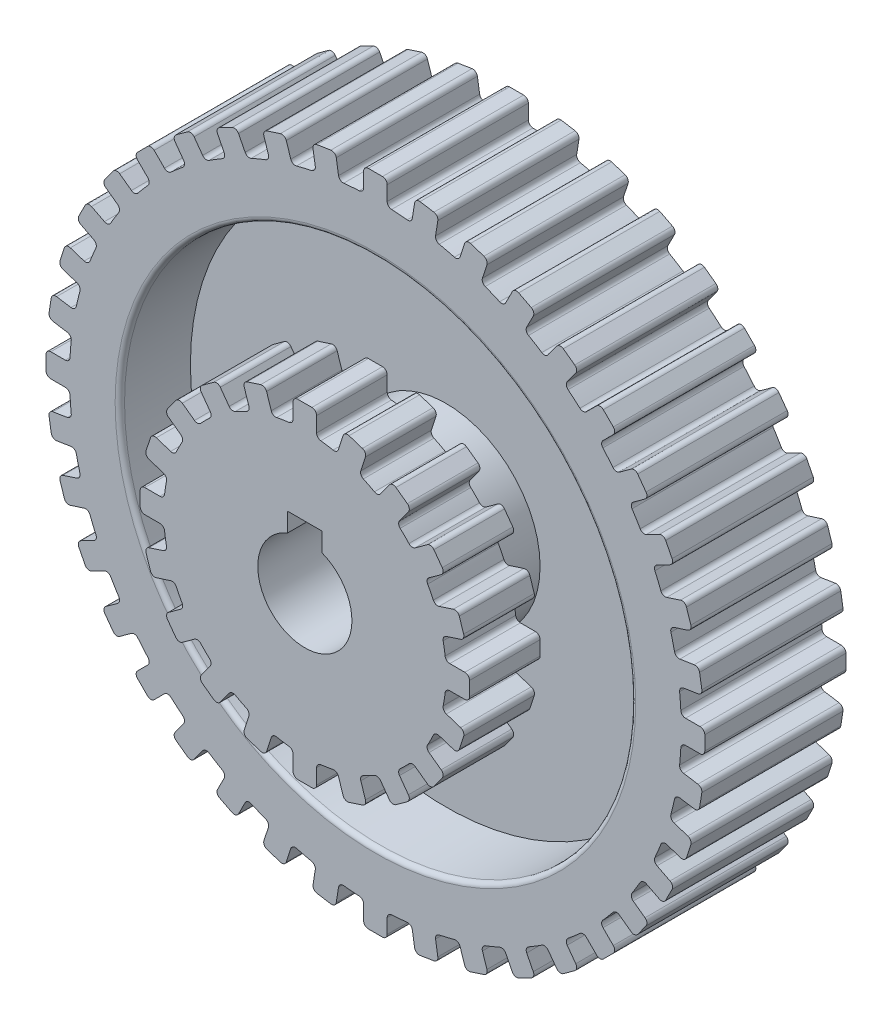
SolidWorks part; units mm, degrees
ref_plane "Front Plane" through (0, 0, 0) normal (0, 0, 1) x (1, 0, 0)
ref_plane "Top Plane" through (0, 0, 0) normal (0, 1, 0) x (1, 0, 0)
ref_plane "Right Plane" through (0, 0, 0) normal (1, 0, 0) x (0, 0, -1)
sketch "Sketch1" plane through (0, 0, 0) normal (0, 0, 1) x (1, 0, 0)
  line L0 (8.3248, 68.5416) -> (7.8409, 65.4868)
  line L1 (-1.5, 70) -> (1.5, 70)
  line L2 (2.5, 69) -> (2.5, 65.9071)
  line L3 (-2.5, 69) -> (-2.5, 65.9071)
  line L4 (9.4689, 69.3728) -> (12.4319, 68.9035)
  line L5 (13.2632, 67.7594) -> (12.7794, 64.7046)
  line L6 (18.9445, 66.3954) -> (17.9888, 63.4539)
  line L7 (20.2046, 67.0375) -> (23.0578, 66.1104)
  line L8 (23.6998, 64.8504) -> (22.7441, 61.9089)
  line L9 (29.0978, 62.6144) -> (27.6937, 59.8587)
  line L10 (30.4428, 63.0514) -> (33.1158, 61.6895)
  line L11 (33.5529, 60.3445) -> (32.1487, 57.5887)
  line L12 (38.5346, 57.2916) -> (36.7167, 54.7895)
  line L13 (39.9314, 57.5129) -> (42.3585, 55.7495)
  line L14 (42.5797, 54.3527) -> (40.7618, 51.8505)
  line L15 (47.0226, 50.5581) -> (44.8356, 48.3711)
  line L16 (48.4368, 50.5581) -> (50.5581, 48.4368)
  line L17 (50.5581, 47.0226) -> (48.3711, 44.8356)
  line L18 (54.3527, 42.5797) -> (51.8505, 40.7618)
  line L19 (55.7495, 42.3585) -> (57.5129, 39.9314)
  line L20 (57.2916, 38.5346) -> (54.7895, 36.7167)
  line L21 (60.3445, 33.5529) -> (57.5887, 32.1487)
  line L22 (61.6895, 33.1158) -> (63.0514, 30.4428)
  line L23 (62.6144, 29.0978) -> (59.8587, 27.6937)
  line L24 (64.8504, 23.6998) -> (61.9089, 22.7441)
  line L25 (66.1104, 23.0578) -> (67.0375, 20.2046)
  line L26 (66.3954, 18.9445) -> (63.4539, 17.9888)
  line L27 (67.7594, 13.2632) -> (64.7046, 12.7794)
  line L28 (68.9035, 12.4319) -> (69.3728, 9.4689)
  line L29 (68.5416, 8.3248) -> (65.4868, 7.8409)
  line L30 (69, 2.5) -> (65.9071, 2.5)
  line L31 (70, 1.5) -> (70, -1.5)
  line L32 (69, -2.5) -> (65.9071, -2.5)
  line L33 (68.5416, -8.3248) -> (65.4868, -7.8409)
  line L34 (69.3728, -9.4689) -> (68.9035, -12.4319)
  line L35 (67.7594, -13.2632) -> (64.7046, -12.7794)
  line L36 (66.3954, -18.9445) -> (63.4539, -17.9888)
  line L37 (67.0375, -20.2046) -> (66.1104, -23.0578)
  line L38 (64.8504, -23.6998) -> (61.9089, -22.7441)
  line L39 (62.6144, -29.0978) -> (59.8587, -27.6937)
  line L40 (63.0514, -30.4428) -> (61.6895, -33.1158)
  line L41 (60.3445, -33.5529) -> (57.5887, -32.1487)
  line L42 (57.2916, -38.5346) -> (54.7895, -36.7167)
  line L43 (57.5129, -39.9314) -> (55.7495, -42.3585)
  line L44 (54.3527, -42.5797) -> (51.8505, -40.7618)
  line L45 (50.5581, -47.0226) -> (48.3711, -44.8356)
  line L46 (50.5581, -48.4368) -> (48.4368, -50.5581)
  line L47 (47.0226, -50.5581) -> (44.8356, -48.3711)
  line L48 (42.5797, -54.3527) -> (40.7618, -51.8505)
  line L49 (42.3585, -55.7495) -> (39.9314, -57.5129)
  line L50 (38.5346, -57.2916) -> (36.7167, -54.7895)
  line L51 (33.5529, -60.3445) -> (32.1487, -57.5887)
  line L52 (33.1158, -61.6895) -> (30.4428, -63.0514)
  line L53 (29.0978, -62.6144) -> (27.6937, -59.8587)
  line L54 (23.6998, -64.8504) -> (22.7441, -61.9089)
  line L55 (23.0578, -66.1104) -> (20.2046, -67.0375)
  line L56 (18.9445, -66.3954) -> (17.9888, -63.4539)
  line L57 (13.2632, -67.7594) -> (12.7794, -64.7046)
  line L58 (12.4319, -68.9035) -> (9.4689, -69.3728)
  line L59 (8.3248, -68.5416) -> (7.8409, -65.4868)
  line L60 (2.5, -69) -> (2.5, -65.9071)
  line L61 (1.5, -70) -> (-1.5, -70)
  line L62 (-2.5, -69) -> (-2.5, -65.9071)
  line L63 (-8.3248, -68.5416) -> (-7.8409, -65.4868)
  line L64 (-9.4689, -69.3728) -> (-12.4319, -68.9035)
  line L65 (-13.2632, -67.7594) -> (-12.7794, -64.7046)
  line L66 (-18.9445, -66.3954) -> (-17.9888, -63.4539)
  line L67 (-20.2046, -67.0375) -> (-23.0578, -66.1104)
  line L68 (-23.6998, -64.8504) -> (-22.7441, -61.9089)
  line L69 (-29.0978, -62.6144) -> (-27.6937, -59.8587)
  line L70 (-30.4428, -63.0514) -> (-33.1158, -61.6895)
  line L71 (-33.5529, -60.3445) -> (-32.1487, -57.5887)
  line L72 (-38.5346, -57.2916) -> (-36.7167, -54.7895)
  line L73 (-39.9314, -57.5129) -> (-42.3585, -55.7495)
  line L74 (-42.5797, -54.3527) -> (-40.7618, -51.8505)
  line L75 (-47.0226, -50.5581) -> (-44.8356, -48.3711)
  line L76 (-48.4368, -50.5581) -> (-50.5581, -48.4368)
  line L77 (-50.5581, -47.0226) -> (-48.3711, -44.8356)
  line L78 (-54.3527, -42.5797) -> (-51.8505, -40.7618)
  line L79 (-55.7495, -42.3585) -> (-57.5129, -39.9314)
  line L80 (-57.2916, -38.5346) -> (-54.7895, -36.7167)
  line L81 (-60.3445, -33.5529) -> (-57.5887, -32.1487)
  line L82 (-61.6895, -33.1158) -> (-63.0514, -30.4428)
  line L83 (-62.6144, -29.0978) -> (-59.8587, -27.6937)
  line L84 (-64.8504, -23.6998) -> (-61.9089, -22.7441)
  line L85 (-66.1104, -23.0578) -> (-67.0375, -20.2046)
  line L86 (-66.3954, -18.9445) -> (-63.4539, -17.9888)
  line L87 (-67.7594, -13.2632) -> (-64.7046, -12.7794)
  line L88 (-68.9035, -12.4319) -> (-69.3728, -9.4689)
  line L89 (-68.5416, -8.3248) -> (-65.4868, -7.8409)
  line L90 (-69, -2.5) -> (-65.9071, -2.5)
  line L91 (-70, -1.5) -> (-70, 1.5)
  line L92 (-69, 2.5) -> (-65.9071, 2.5)
  line L93 (-68.5416, 8.3248) -> (-65.4868, 7.8409)
  line L94 (-69.3728, 9.4689) -> (-68.9035, 12.4319)
  line L95 (-67.7594, 13.2632) -> (-64.7046, 12.7794)
  line L96 (-66.3954, 18.9445) -> (-63.4539, 17.9888)
  line L97 (-67.0375, 20.2046) -> (-66.1104, 23.0578)
  line L98 (-64.8504, 23.6998) -> (-61.9089, 22.7441)
  line L99 (-62.6144, 29.0978) -> (-59.8587, 27.6937)
  line L100 (-63.0514, 30.4428) -> (-61.6895, 33.1158)
  line L101 (-60.3445, 33.5529) -> (-57.5887, 32.1487)
  line L102 (-57.2916, 38.5346) -> (-54.7895, 36.7167)
  line L103 (-57.5129, 39.9314) -> (-55.7495, 42.3585)
  line L104 (-54.3527, 42.5797) -> (-51.8505, 40.7618)
  line L105 (-50.5581, 47.0226) -> (-48.3711, 44.8356)
  line L106 (-50.5581, 48.4368) -> (-48.4368, 50.5581)
  line L107 (-47.0226, 50.5581) -> (-44.8356, 48.3711)
  line L108 (-42.5797, 54.3527) -> (-40.7618, 51.8505)
  line L109 (-42.3585, 55.7495) -> (-39.9314, 57.5129)
  line L110 (-38.5346, 57.2916) -> (-36.7167, 54.7895)
  line L111 (-33.5529, 60.3445) -> (-32.1487, 57.5887)
  line L112 (-33.1158, 61.6895) -> (-30.4428, 63.0514)
  line L113 (-29.0978, 62.6144) -> (-27.6937, 59.8587)
  line L114 (-23.6998, 64.8504) -> (-22.7441, 61.9089)
  line L115 (-23.0578, 66.1104) -> (-20.2046, 67.0375)
  line L116 (-18.9445, 66.3954) -> (-17.9888, 63.4539)
  line L117 (-13.2632, 67.7594) -> (-12.7794, 64.7046)
  line L118 (-12.4319, 68.9035) -> (-9.4689, 69.3728)
  line L119 (-8.3248, 68.5416) -> (-7.8409, 65.4868)
  arc A0 (-3.447, 64.9085) -> (-6.7494, 64.6486) centre (0, 0) ccw
  arc A2 (-2.5, 65.9071) -> (-3.447, 64.9085) centre (-3.5, 65.9071) cw
  arc A3 (3.447, 64.9085) -> (2.5, 65.9071) centre (3.5, 65.9071) cw
  arc A4 (1.5, 70) -> (2.5, 69) centre (1.5, 69) cw
  arc A5 (-1.5, 70) -> (-2.5, 69) centre (-1.5, 69) ccw
  arc A6 (7.8409, 65.4868) -> (6.7494, 64.6486) centre (6.8532, 65.6432) cw
  arc A7 (9.4689, 69.3728) -> (8.3248, 68.5416) centre (9.3124, 68.3851) ccw
  arc A8 (12.4319, 68.9035) -> (13.2632, 67.7594) centre (12.2755, 67.9158) cw
  arc A9 (13.5585, 63.5702) -> (12.7794, 64.7046) centre (13.7671, 64.5482) cw
  arc A10 (17.9888, 63.4539) -> (16.7796, 62.7969) centre (17.0377, 63.763) cw
  arc A11 (20.2046, 67.0375) -> (18.9445, 66.3954) centre (19.8956, 66.0864) ccw
  arc A12 (23.0578, 66.1104) -> (23.6998, 64.8504) centre (22.7488, 65.1594) cw
  arc A13 (23.3361, 60.6665) -> (22.7441, 61.9089) centre (23.6951, 61.5998) cw
  arc A14 (27.6937, 59.8587) -> (26.3966, 59.3988) centre (26.8027, 60.3127) cw
  arc A15 (30.4428, 63.0514) -> (29.0978, 62.6144) centre (29.9888, 62.1604) ccw
  arc A16 (33.1158, 61.6895) -> (33.5529, 60.3445) centre (32.6619, 60.7985) cw
  arc A17 (32.5391, 56.269) -> (32.1487, 57.5887) centre (33.0397, 57.1347) cw
  arc A18 (36.7167, 54.7895) -> (35.3636, 54.5382) centre (35.9077, 55.3772) cw
  arc A19 (39.9314, 57.5129) -> (38.5346, 57.2916) centre (39.3437, 56.7039) ccw
  arc A20 (42.3585, 55.7495) -> (42.5797, 54.3527) centre (41.7707, 54.9405) cw
  arc A21 (40.9409, 50.486) -> (40.7618, 51.8505) centre (41.5708, 51.2627) cw
  arc A22 (44.8356, 48.3711) -> (43.4599, 48.3346) centre (44.1285, 49.0783) cw
  arc A23 (48.4368, 50.5581) -> (47.0226, 50.5581) centre (47.7297, 49.851) ccw
  arc A24 (50.5581, 48.4368) -> (50.5581, 47.0226) centre (49.851, 47.7297) cw
  arc A25 (48.3346, 43.4599) -> (48.3711, 44.8356) centre (49.0783, 44.1285) cw
  arc A26 (51.8505, 40.7618) -> (50.486, 40.9409) centre (51.2627, 41.5708) cw
  arc A27 (55.7495, 42.3585) -> (54.3527, 42.5797) centre (54.9405, 41.7707) ccw
  arc A28 (57.5129, 39.9314) -> (57.2916, 38.5346) centre (56.7039, 39.3437) cw
  arc A29 (54.5382, 35.3636) -> (54.7895, 36.7167) centre (55.3772, 35.9077) cw
  arc A30 (57.5887, 32.1487) -> (56.269, 32.5391) centre (57.1347, 33.0397) cw
  arc A31 (61.6895, 33.1158) -> (60.3445, 33.5529) centre (60.7985, 32.6619) ccw
  arc A32 (63.0514, 30.4428) -> (62.6144, 29.0978) centre (62.1604, 29.9888) cw
  arc A33 (59.3988, 26.3966) -> (59.8587, 27.6937) centre (60.3127, 26.8027) cw
  arc A34 (61.9089, 22.7441) -> (60.6665, 23.3361) centre (61.5998, 23.6951) cw
  arc A35 (66.1104, 23.0578) -> (64.8504, 23.6998) centre (65.1594, 22.7488) ccw
  arc A36 (67.0375, 20.2046) -> (66.3954, 18.9445) centre (66.0864, 19.8956) cw
  arc A37 (62.7969, 16.7796) -> (63.4539, 17.9888) centre (63.763, 17.0377) cw
  arc A38 (64.7046, 12.7794) -> (63.5702, 13.5585) centre (64.5482, 13.7671) cw
  arc A39 (68.9035, 12.4319) -> (67.7594, 13.2632) centre (67.9158, 12.2755) ccw
  arc A40 (69.3728, 9.4689) -> (68.5416, 8.3248) centre (68.3851, 9.3124) cw
  arc A41 (64.6486, 6.7494) -> (65.4868, 7.8409) centre (65.6432, 6.8532) cw
  arc A42 (65.9071, 2.5) -> (64.9085, 3.447) centre (65.9071, 3.5) cw
  arc A43 (70, 1.5) -> (69, 2.5) centre (69, 1.5) ccw
  arc A44 (70, -1.5) -> (69, -2.5) centre (69, -1.5) cw
  arc A45 (64.9085, -3.447) -> (65.9071, -2.5) centre (65.9071, -3.5) cw
  arc A46 (65.4868, -7.8409) -> (64.6486, -6.7494) centre (65.6432, -6.8532) cw
  arc A47 (69.3728, -9.4689) -> (68.5416, -8.3248) centre (68.3851, -9.3124) ccw
  arc A48 (68.9035, -12.4319) -> (67.7594, -13.2632) centre (67.9158, -12.2755) cw
  arc A49 (63.5702, -13.5585) -> (64.7046, -12.7794) centre (64.5482, -13.7671) cw
  arc A50 (63.4539, -17.9888) -> (62.7969, -16.7796) centre (63.763, -17.0377) cw
  arc A51 (67.0375, -20.2046) -> (66.3954, -18.9445) centre (66.0864, -19.8956) ccw
  arc A52 (66.1104, -23.0578) -> (64.8504, -23.6998) centre (65.1594, -22.7488) cw
  arc A53 (60.6665, -23.3361) -> (61.9089, -22.7441) centre (61.5998, -23.6951) cw
  arc A54 (59.8587, -27.6937) -> (59.3988, -26.3966) centre (60.3127, -26.8027) cw
  arc A55 (63.0514, -30.4428) -> (62.6144, -29.0978) centre (62.1604, -29.9888) ccw
  arc A56 (61.6895, -33.1158) -> (60.3445, -33.5529) centre (60.7985, -32.6619) cw
  arc A57 (56.269, -32.5391) -> (57.5887, -32.1487) centre (57.1347, -33.0397) cw
  arc A58 (54.7895, -36.7167) -> (54.5382, -35.3636) centre (55.3772, -35.9077) cw
  arc A59 (57.5129, -39.9314) -> (57.2916, -38.5346) centre (56.7039, -39.3437) ccw
  arc A60 (55.7495, -42.3585) -> (54.3527, -42.5797) centre (54.9405, -41.7707) cw
  arc A61 (50.486, -40.9409) -> (51.8505, -40.7618) centre (51.2627, -41.5708) cw
  arc A62 (48.3711, -44.8356) -> (48.3346, -43.4599) centre (49.0783, -44.1285) cw
  arc A63 (50.5581, -48.4368) -> (50.5581, -47.0226) centre (49.851, -47.7297) ccw
  arc A64 (48.4368, -50.5581) -> (47.0226, -50.5581) centre (47.7297, -49.851) cw
  arc A65 (43.4599, -48.3346) -> (44.8356, -48.3711) centre (44.1285, -49.0783) cw
  arc A66 (40.7618, -51.8505) -> (40.9409, -50.486) centre (41.5708, -51.2627) cw
  arc A67 (42.3585, -55.7495) -> (42.5797, -54.3527) centre (41.7707, -54.9405) ccw
  arc A68 (39.9314, -57.5129) -> (38.5346, -57.2916) centre (39.3437, -56.7039) cw
  arc A69 (35.3636, -54.5382) -> (36.7167, -54.7895) centre (35.9077, -55.3772) cw
  arc A70 (32.1487, -57.5887) -> (32.5391, -56.269) centre (33.0397, -57.1347) cw
  arc A71 (33.1158, -61.6895) -> (33.5529, -60.3445) centre (32.6619, -60.7985) ccw
  arc A72 (30.4428, -63.0514) -> (29.0978, -62.6144) centre (29.9888, -62.1604) cw
  arc A73 (26.3966, -59.3988) -> (27.6937, -59.8587) centre (26.8027, -60.3127) cw
  arc A74 (22.7441, -61.9089) -> (23.3361, -60.6665) centre (23.6951, -61.5998) cw
  arc A75 (23.0578, -66.1104) -> (23.6998, -64.8504) centre (22.7488, -65.1594) ccw
  arc A76 (20.2046, -67.0375) -> (18.9445, -66.3954) centre (19.8956, -66.0864) cw
  arc A77 (16.7796, -62.7969) -> (17.9888, -63.4539) centre (17.0377, -63.763) cw
  arc A78 (12.7794, -64.7046) -> (13.5585, -63.5702) centre (13.7671, -64.5482) cw
  arc A79 (12.4319, -68.9035) -> (13.2632, -67.7594) centre (12.2755, -67.9158) ccw
  arc A80 (9.4689, -69.3728) -> (8.3248, -68.5416) centre (9.3124, -68.3851) cw
  arc A81 (6.7494, -64.6486) -> (7.8409, -65.4868) centre (6.8532, -65.6432) cw
  arc A82 (2.5, -65.9071) -> (3.447, -64.9085) centre (3.5, -65.9071) cw
  arc A83 (1.5, -70) -> (2.5, -69) centre (1.5, -69) ccw
  arc A84 (-1.5, -70) -> (-2.5, -69) centre (-1.5, -69) cw
  arc A85 (-3.447, -64.9085) -> (-2.5, -65.9071) centre (-3.5, -65.9071) cw
  arc A86 (-7.8409, -65.4868) -> (-6.7494, -64.6486) centre (-6.8532, -65.6432) cw
  arc A87 (-9.4689, -69.3728) -> (-8.3248, -68.5416) centre (-9.3124, -68.3851) ccw
  arc A88 (-12.4319, -68.9035) -> (-13.2632, -67.7594) centre (-12.2755, -67.9158) cw
  arc A89 (-13.5585, -63.5702) -> (-12.7794, -64.7046) centre (-13.7671, -64.5482) cw
  arc A90 (-17.9888, -63.4539) -> (-16.7796, -62.7969) centre (-17.0377, -63.763) cw
  arc A91 (-20.2046, -67.0375) -> (-18.9445, -66.3954) centre (-19.8956, -66.0864) ccw
  arc A92 (-23.0578, -66.1104) -> (-23.6998, -64.8504) centre (-22.7488, -65.1594) cw
  arc A93 (-23.3361, -60.6665) -> (-22.7441, -61.9089) centre (-23.6951, -61.5998) cw
  arc A94 (-27.6937, -59.8587) -> (-26.3966, -59.3988) centre (-26.8027, -60.3127) cw
  arc A95 (-30.4428, -63.0514) -> (-29.0978, -62.6144) centre (-29.9888, -62.1604) ccw
  arc A96 (-33.1158, -61.6895) -> (-33.5529, -60.3445) centre (-32.6619, -60.7985) cw
  arc A97 (-32.5391, -56.269) -> (-32.1487, -57.5887) centre (-33.0397, -57.1347) cw
  arc A98 (-36.7167, -54.7895) -> (-35.3636, -54.5382) centre (-35.9077, -55.3772) cw
  arc A99 (-39.9314, -57.5129) -> (-38.5346, -57.2916) centre (-39.3437, -56.7039) ccw
  arc A100 (-42.3585, -55.7495) -> (-42.5797, -54.3527) centre (-41.7707, -54.9405) cw
  arc A101 (-40.9409, -50.486) -> (-40.7618, -51.8505) centre (-41.5708, -51.2627) cw
  arc A102 (-44.8356, -48.3711) -> (-43.4599, -48.3346) centre (-44.1285, -49.0783) cw
  arc A103 (-48.4368, -50.5581) -> (-47.0226, -50.5581) centre (-47.7297, -49.851) ccw
  arc A104 (-50.5581, -48.4368) -> (-50.5581, -47.0226) centre (-49.851, -47.7297) cw
  arc A105 (-48.3346, -43.4599) -> (-48.3711, -44.8356) centre (-49.0783, -44.1285) cw
  arc A106 (-51.8505, -40.7618) -> (-50.486, -40.9409) centre (-51.2627, -41.5708) cw
  arc A107 (-55.7495, -42.3585) -> (-54.3527, -42.5797) centre (-54.9405, -41.7707) ccw
  arc A108 (-57.5129, -39.9314) -> (-57.2916, -38.5346) centre (-56.7039, -39.3437) cw
  arc A109 (-54.5382, -35.3636) -> (-54.7895, -36.7167) centre (-55.3772, -35.9077) cw
  arc A110 (-57.5887, -32.1487) -> (-56.269, -32.5391) centre (-57.1347, -33.0397) cw
  arc A111 (-61.6895, -33.1158) -> (-60.3445, -33.5529) centre (-60.7985, -32.6619) ccw
  arc A112 (-63.0514, -30.4428) -> (-62.6144, -29.0978) centre (-62.1604, -29.9888) cw
  arc A113 (-59.3988, -26.3966) -> (-59.8587, -27.6937) centre (-60.3127, -26.8027) cw
  arc A114 (-61.9089, -22.7441) -> (-60.6665, -23.3361) centre (-61.5998, -23.6951) cw
  arc A115 (-66.1104, -23.0578) -> (-64.8504, -23.6998) centre (-65.1594, -22.7488) ccw
  arc A116 (-67.0375, -20.2046) -> (-66.3954, -18.9445) centre (-66.0864, -19.8956) cw
  arc A117 (-62.7969, -16.7796) -> (-63.4539, -17.9888) centre (-63.763, -17.0377) cw
  arc A118 (-64.7046, -12.7794) -> (-63.5702, -13.5585) centre (-64.5482, -13.7671) cw
  arc A119 (-68.9035, -12.4319) -> (-67.7594, -13.2632) centre (-67.9158, -12.2755) ccw
  arc A120 (-69.3728, -9.4689) -> (-68.5416, -8.3248) centre (-68.3851, -9.3124) cw
  arc A121 (-64.6486, -6.7494) -> (-65.4868, -7.8409) centre (-65.6432, -6.8532) cw
  arc A122 (-65.9071, -2.5) -> (-64.9085, -3.447) centre (-65.9071, -3.5) cw
  arc A123 (-70, -1.5) -> (-69, -2.5) centre (-69, -1.5) ccw
  arc A124 (-70, 1.5) -> (-69, 2.5) centre (-69, 1.5) cw
  arc A125 (-64.9085, 3.447) -> (-65.9071, 2.5) centre (-65.9071, 3.5) cw
  arc A126 (-65.4868, 7.8409) -> (-64.6486, 6.7494) centre (-65.6432, 6.8532) cw
  arc A127 (-69.3728, 9.4689) -> (-68.5416, 8.3248) centre (-68.3851, 9.3124) ccw
  arc A128 (-68.9035, 12.4319) -> (-67.7594, 13.2632) centre (-67.9158, 12.2755) cw
  arc A129 (-63.5702, 13.5585) -> (-64.7046, 12.7794) centre (-64.5482, 13.7671) cw
  arc A130 (-63.4539, 17.9888) -> (-62.7969, 16.7796) centre (-63.763, 17.0377) cw
  arc A131 (-67.0375, 20.2046) -> (-66.3954, 18.9445) centre (-66.0864, 19.8956) ccw
  arc A132 (-66.1104, 23.0578) -> (-64.8504, 23.6998) centre (-65.1594, 22.7488) cw
  arc A133 (-60.6665, 23.3361) -> (-61.9089, 22.7441) centre (-61.5998, 23.6951) cw
  arc A134 (-59.8587, 27.6937) -> (-59.3988, 26.3966) centre (-60.3127, 26.8027) cw
  arc A135 (-63.0514, 30.4428) -> (-62.6144, 29.0978) centre (-62.1604, 29.9888) ccw
  arc A136 (-61.6895, 33.1158) -> (-60.3445, 33.5529) centre (-60.7985, 32.6619) cw
  arc A137 (-56.269, 32.5391) -> (-57.5887, 32.1487) centre (-57.1347, 33.0397) cw
  arc A138 (-54.7895, 36.7167) -> (-54.5382, 35.3636) centre (-55.3772, 35.9077) cw
  arc A139 (-57.5129, 39.9314) -> (-57.2916, 38.5346) centre (-56.7039, 39.3437) ccw
  arc A140 (-55.7495, 42.3585) -> (-54.3527, 42.5797) centre (-54.9405, 41.7707) cw
  arc A141 (-50.486, 40.9409) -> (-51.8505, 40.7618) centre (-51.2627, 41.5708) cw
  arc A142 (-48.3711, 44.8356) -> (-48.3346, 43.4599) centre (-49.0783, 44.1285) cw
  arc A143 (-50.5581, 48.4368) -> (-50.5581, 47.0226) centre (-49.851, 47.7297) ccw
  arc A144 (-48.4368, 50.5581) -> (-47.0226, 50.5581) centre (-47.7297, 49.851) cw
  arc A145 (-43.4599, 48.3346) -> (-44.8356, 48.3711) centre (-44.1285, 49.0783) cw
  arc A146 (-40.7618, 51.8505) -> (-40.9409, 50.486) centre (-41.5708, 51.2627) cw
  arc A147 (-42.3585, 55.7495) -> (-42.5797, 54.3527) centre (-41.7707, 54.9405) ccw
  arc A148 (-39.9314, 57.5129) -> (-38.5346, 57.2916) centre (-39.3437, 56.7039) cw
  arc A149 (-35.3636, 54.5382) -> (-36.7167, 54.7895) centre (-35.9077, 55.3772) cw
  arc A150 (-32.1487, 57.5887) -> (-32.5391, 56.269) centre (-33.0397, 57.1347) cw
  arc A151 (-33.1158, 61.6895) -> (-33.5529, 60.3445) centre (-32.6619, 60.7985) ccw
  arc A152 (-30.4428, 63.0514) -> (-29.0978, 62.6144) centre (-29.9888, 62.1604) cw
  arc A153 (-26.3966, 59.3988) -> (-27.6937, 59.8587) centre (-26.8027, 60.3127) cw
  arc A154 (-22.7441, 61.9089) -> (-23.3361, 60.6665) centre (-23.6951, 61.5998) cw
  arc A155 (-23.0578, 66.1104) -> (-23.6998, 64.8504) centre (-22.7488, 65.1594) ccw
  arc A156 (-20.2046, 67.0375) -> (-18.9445, 66.3954) centre (-19.8956, 66.0864) cw
  arc A157 (-16.7796, 62.7969) -> (-17.9888, 63.4539) centre (-17.0377, 63.763) cw
  arc A158 (-12.7794, 64.7046) -> (-13.5585, 63.5702) centre (-13.7671, 64.5482) cw
  arc A159 (-12.4319, 68.9035) -> (-13.2632, 67.7594) centre (-12.2755, 67.9158) ccw
  arc A160 (-9.4689, 69.3728) -> (-8.3248, 68.5416) centre (-9.3124, 68.3851) cw
  arc A161 (-6.7494, 64.6486) -> (-7.8409, 65.4868) centre (-6.8532, 65.6432) cw
  arc A162 (-13.5585, 63.5702) -> (-16.7796, 62.7969) centre (0, 0) ccw
  arc A163 (6.7494, 64.6486) -> (3.447, 64.9085) centre (0, 0) ccw
  arc A164 (16.7796, 62.7969) -> (13.5585, 63.5702) centre (0, 0) ccw
  arc A165 (26.3966, 59.3988) -> (23.3361, 60.6665) centre (0, 0) ccw
  arc A166 (-23.3361, 60.6665) -> (-26.3966, 59.3988) centre (0, 0) ccw
  arc A167 (-32.5391, 56.269) -> (-35.3636, 54.5382) centre (0, 0) ccw
  arc A168 (-40.9409, 50.486) -> (-43.4599, 48.3346) centre (0, 0) ccw
  arc A169 (-48.3346, 43.4599) -> (-50.486, 40.9409) centre (0, 0) ccw
  arc A170 (-54.5382, 35.3636) -> (-56.269, 32.5391) centre (0, 0) ccw
  arc A171 (35.3636, 54.5382) -> (32.5391, 56.269) centre (0, 0) ccw
  arc A172 (43.4599, 48.3346) -> (40.9409, 50.486) centre (0, 0) ccw
  arc A173 (50.486, 40.9409) -> (48.3346, 43.4599) centre (0, 0) ccw
  arc A174 (56.269, 32.5391) -> (54.5382, 35.3636) centre (0, 0) ccw
  arc A175 (60.6665, 23.3361) -> (59.3988, 26.3966) centre (0, 0) ccw
  arc A176 (63.5702, 13.5585) -> (62.7969, 16.7796) centre (0, 0) ccw
  arc A177 (64.9085, 3.447) -> (64.6486, 6.7494) centre (0, 0) ccw
  arc A178 (64.6486, -6.7494) -> (64.9085, -3.447) centre (0, 0) ccw
  arc A179 (62.7969, -16.7796) -> (63.5702, -13.5585) centre (0, 0) ccw
  arc A180 (59.3988, -26.3966) -> (60.6665, -23.3361) centre (0, 0) ccw
  arc A181 (54.5382, -35.3636) -> (56.269, -32.5391) centre (0, 0) ccw
  arc A182 (48.3346, -43.4599) -> (50.486, -40.9409) centre (0, 0) ccw
  arc A183 (40.9409, -50.486) -> (43.4599, -48.3346) centre (0, 0) ccw
  arc A184 (32.5391, -56.269) -> (35.3636, -54.5382) centre (0, 0) ccw
  arc A185 (23.3361, -60.6665) -> (26.3966, -59.3988) centre (0, 0) ccw
  arc A186 (13.5585, -63.5702) -> (16.7796, -62.7969) centre (0, 0) ccw
  arc A187 (3.447, -64.9085) -> (6.7494, -64.6486) centre (0, 0) ccw
  arc A188 (-6.7494, -64.6486) -> (-3.447, -64.9085) centre (0, 0) ccw
  arc A189 (-16.7796, -62.7969) -> (-13.5585, -63.5702) centre (0, 0) ccw
  arc A190 (-26.3966, -59.3988) -> (-23.3361, -60.6665) centre (0, 0) ccw
  arc A191 (-35.3636, -54.5382) -> (-32.5391, -56.269) centre (0, 0) ccw
  arc A192 (-43.4599, -48.3346) -> (-40.9409, -50.486) centre (0, 0) ccw
  arc A193 (-50.486, -40.9409) -> (-48.3346, -43.4599) centre (0, 0) ccw
  arc A194 (-56.269, -32.5391) -> (-54.5382, -35.3636) centre (0, 0) ccw
  arc A195 (-60.6665, -23.3361) -> (-59.3988, -26.3966) centre (0, 0) ccw
  arc A196 (-63.5702, -13.5585) -> (-62.7969, -16.7796) centre (0, 0) ccw
  arc A197 (-64.9085, -3.447) -> (-64.6486, -6.7494) centre (0, 0) ccw
  arc A198 (-64.6486, 6.7494) -> (-64.9085, 3.447) centre (0, 0) ccw
  arc A199 (-62.7969, 16.7796) -> (-63.5702, 13.5585) centre (0, 0) ccw
  arc A200 (-59.3988, 26.3966) -> (-60.6665, 23.3361) centre (0, 0) ccw
  point P486 (0, 0)
  dimension "D1" = 1
  dimension "D2" = 40
extrude "Boss-Extrude1" add sketch "Sketch1" along normal blind 30
sketch "Sketch2" plane through (0, 0, 30) normal (0, 0, 1) x (1, 0, 0)
  line L1 (-3.5387, 13.1147) -> (3.5387, 13.1147)
  line L2 (-3.5387, 13.1147) -> (-3.5387, 9.353)
  line L4 (3.5387, 13.1147) -> (3.5387, 9.353)
  circle A0 centre (0, 0) radius 20
  arc A1 (-3.5387, 9.353) -> (3.5387, 9.353) centre (0, 0) ccw
extrude "Cut-Extrude1" cut sketch "Sketch2" against normal blind 30 contours A1 L4 L1 L2
sketch "Sketch3" plane through (0, 0, 30) normal (0, 0, 1) x (1, 0, 0)
  circle A0 centre (0, 0) radius 20
  circle A1 centre (0, 0) radius 54.3215
extrude "Cut-Extrude2" cut sketch "Sketch3" against normal blind 15
fillet "Fillet2" radius 1 1 edges at (54.3215, 0, 30)
sketch "Sketch4" plane through (0, 0, 30) normal (0, 0, 1) x (1, 0, 0)
  line L0 (8.1289, 33.1085) -> (7.1406, 30.0668)
  line L1 (-1.5, 35) -> (1.5, 35)
  line L2 (2.5, 34) -> (2.5, 30.8018)
  line L3 (-2.5, 34) -> (-2.5, 30.8018)
  line L4 (9.389, 33.7505) -> (12.2422, 32.8235)
  line L5 (12.8842, 31.5634) -> (11.8959, 28.5217)
  line L6 (17.9622, 28.976) -> (16.0823, 26.3886)
  line L7 (19.359, 29.1973) -> (21.786, 27.4339)
  line L8 (22.0072, 26.0371) -> (20.1274, 23.4497)
  line L9 (26.0371, 22.0072) -> (23.4497, 20.1274)
  line L10 (27.4339, 21.786) -> (29.1973, 19.359)
  line L11 (28.976, 17.9622) -> (26.3886, 16.0823)
  line L12 (31.5634, 12.8842) -> (28.5217, 11.8959)
  line L13 (32.8235, 12.2422) -> (33.7505, 9.389)
  line L14 (33.1085, 8.1289) -> (30.0668, 7.1406)
  line L15 (34, 2.5) -> (30.8018, 2.5)
  line L16 (35, 1.5) -> (35, -1.5)
  line L17 (34, -2.5) -> (30.8018, -2.5)
  line L18 (33.1085, -8.1289) -> (30.0668, -7.1406)
  line L19 (33.7505, -9.389) -> (32.8235, -12.2422)
  line L20 (31.5634, -12.8842) -> (28.5217, -11.8959)
  line L21 (28.976, -17.9622) -> (26.3886, -16.0823)
  line L22 (29.1973, -19.359) -> (27.4339, -21.786)
  line L23 (26.0371, -22.0072) -> (23.4497, -20.1274)
  line L24 (22.0072, -26.0371) -> (20.1274, -23.4497)
  line L25 (21.786, -27.4339) -> (19.359, -29.1973)
  line L26 (17.9622, -28.976) -> (16.0823, -26.3886)
  line L27 (12.8842, -31.5634) -> (11.8959, -28.5217)
  line L28 (12.2422, -32.8235) -> (9.389, -33.7505)
  line L29 (8.1289, -33.1085) -> (7.1406, -30.0668)
  line L30 (2.5, -34) -> (2.5, -30.8018)
  line L31 (1.5, -35) -> (-1.5, -35)
  line L32 (-2.5, -34) -> (-2.5, -30.8018)
  line L33 (-8.1289, -33.1085) -> (-7.1406, -30.0668)
  line L34 (-9.389, -33.7505) -> (-12.2422, -32.8235)
  line L35 (-12.8842, -31.5634) -> (-11.8959, -28.5217)
  line L36 (-17.9622, -28.976) -> (-16.0823, -26.3886)
  line L37 (-19.359, -29.1973) -> (-21.786, -27.4339)
  line L38 (-22.0072, -26.0371) -> (-20.1274, -23.4497)
  line L39 (-26.0371, -22.0072) -> (-23.4497, -20.1274)
  line L40 (-27.4339, -21.786) -> (-29.1973, -19.359)
  line L41 (-28.976, -17.9622) -> (-26.3886, -16.0823)
  line L42 (-31.5634, -12.8842) -> (-28.5217, -11.8959)
  line L43 (-32.8235, -12.2422) -> (-33.7505, -9.389)
  line L44 (-33.1085, -8.1289) -> (-30.0668, -7.1406)
  line L45 (-34, -2.5) -> (-30.8018, -2.5)
  line L46 (-35, -1.5) -> (-35, 1.5)
  line L47 (-34, 2.5) -> (-30.8018, 2.5)
  line L48 (-33.1085, 8.1289) -> (-30.0668, 7.1406)
  line L49 (-33.7505, 9.389) -> (-32.8235, 12.2422)
  line L50 (-31.5634, 12.8842) -> (-28.5217, 11.8959)
  line L51 (-28.976, 17.9622) -> (-26.3886, 16.0823)
  line L52 (-29.1973, 19.359) -> (-27.4339, 21.786)
  line L53 (-26.0371, 22.0072) -> (-23.4497, 20.1274)
  line L54 (-22.0072, 26.0371) -> (-20.1274, 23.4497)
  line L55 (-21.786, 27.4339) -> (-19.359, 29.1973)
  line L56 (-17.9622, 28.976) -> (-16.0823, 26.3886)
  line L57 (-12.8842, 31.5634) -> (-11.8959, 28.5217)
  line L58 (-12.2422, 32.8235) -> (-9.389, 33.7505)
  line L59 (-8.1289, 33.1085) -> (-7.1406, 30.0668)
  arc A0 (-3.3871, 29.8082) -> (-5.9899, 29.3959) centre (0, 0) ccw
  arc A2 (2.5, 30.8018) -> (3.3871, 29.8082) centre (3.5, 30.8018) ccw
  arc A3 (2.5, 34) -> (1.5, 35) centre (1.5, 34) ccw
  arc A4 (-1.5, 35) -> (-2.5, 34) centre (-1.5, 34) ccw
  arc A5 (-2.5, 30.8018) -> (-3.3871, 29.8082) centre (-3.5, 30.8018) cw
  arc A6 (7.1406, 30.0668) -> (5.9899, 29.3959) centre (6.1896, 30.3758) cw
  arc A7 (9.389, 33.7505) -> (8.1289, 33.1085) centre (9.08, 32.7994) ccw
  arc A8 (12.8842, 31.5634) -> (12.2422, 32.8235) centre (11.9332, 31.8724) ccw
  arc A9 (11.8959, 28.5217) -> (12.4326, 27.3026) centre (12.847, 28.2127) ccw
  arc A10 (16.0823, 26.3886) -> (14.7806, 26.1062) centre (15.2733, 26.9764) cw
  arc A11 (19.359, 29.1973) -> (17.9622, 28.976) centre (18.7712, 28.3883) ccw
  arc A12 (22.0072, 26.0371) -> (21.786, 27.4339) centre (21.1982, 26.6249) ccw
  arc A13 (20.1274, 23.4497) -> (20.261, 22.1244) centre (20.9364, 22.8619) ccw
  arc A14 (23.4497, 20.1274) -> (22.1244, 20.261) centre (22.8619, 20.9364) cw
  arc A15 (27.4339, 21.786) -> (26.0371, 22.0072) centre (26.6249, 21.1982) ccw
  arc A16 (28.976, 17.9622) -> (29.1973, 19.359) centre (28.3883, 18.7712) ccw
  arc A17 (26.3886, 16.0823) -> (26.1062, 14.7806) centre (26.9764, 15.2733) ccw
  arc A18 (28.5217, 11.8959) -> (27.3026, 12.4326) centre (28.2127, 12.847) cw
  arc A19 (32.8235, 12.2422) -> (31.5634, 12.8842) centre (31.8724, 11.9332) ccw
  arc A20 (33.1085, 8.1289) -> (33.7505, 9.389) centre (32.7994, 9.08) ccw
  arc A21 (30.0668, 7.1406) -> (29.3959, 5.9899) centre (30.3758, 6.1896) ccw
  arc A22 (30.8018, 2.5) -> (29.8082, 3.3871) centre (30.8018, 3.5) cw
  arc A23 (35, 1.5) -> (34, 2.5) centre (34, 1.5) ccw
  arc A24 (34, -2.5) -> (35, -1.5) centre (34, -1.5) ccw
  arc A25 (30.8018, -2.5) -> (29.8082, -3.3871) centre (30.8018, -3.5) ccw
  arc A26 (30.0668, -7.1406) -> (29.3959, -5.9899) centre (30.3758, -6.1896) cw
  arc A27 (33.7505, -9.389) -> (33.1085, -8.1289) centre (32.7994, -9.08) ccw
  arc A28 (31.5634, -12.8842) -> (32.8235, -12.2422) centre (31.8724, -11.9332) ccw
  arc A29 (28.5217, -11.8959) -> (27.3026, -12.4326) centre (28.2127, -12.847) ccw
  arc A30 (26.3886, -16.0823) -> (26.1062, -14.7806) centre (26.9764, -15.2733) cw
  arc A31 (29.1973, -19.359) -> (28.976, -17.9622) centre (28.3883, -18.7712) ccw
  arc A32 (26.0371, -22.0072) -> (27.4339, -21.786) centre (26.6249, -21.1982) ccw
  arc A33 (23.4497, -20.1274) -> (22.1244, -20.261) centre (22.8619, -20.9364) ccw
  arc A34 (20.1274, -23.4497) -> (20.261, -22.1244) centre (20.9364, -22.8619) cw
  arc A35 (21.786, -27.4339) -> (22.0072, -26.0371) centre (21.1982, -26.6249) ccw
  arc A36 (17.9622, -28.976) -> (19.359, -29.1973) centre (18.7712, -28.3883) ccw
  arc A37 (16.0823, -26.3886) -> (14.7806, -26.1062) centre (15.2733, -26.9764) ccw
  arc A38 (11.8959, -28.5217) -> (12.4326, -27.3026) centre (12.847, -28.2127) cw
  arc A39 (12.2422, -32.8235) -> (12.8842, -31.5634) centre (11.9332, -31.8724) ccw
  arc A40 (8.1289, -33.1085) -> (9.389, -33.7505) centre (9.08, -32.7994) ccw
  arc A41 (7.1406, -30.0668) -> (5.9899, -29.3959) centre (6.1896, -30.3758) ccw
  arc A42 (2.5, -30.8018) -> (3.3871, -29.8082) centre (3.5, -30.8018) cw
  arc A43 (1.5, -35) -> (2.5, -34) centre (1.5, -34) ccw
  arc A44 (-2.5, -34) -> (-1.5, -35) centre (-1.5, -34) ccw
  arc A45 (-2.5, -30.8018) -> (-3.3871, -29.8082) centre (-3.5, -30.8018) ccw
  arc A46 (-7.1406, -30.0668) -> (-5.9899, -29.3959) centre (-6.1896, -30.3758) cw
  arc A47 (-9.389, -33.7505) -> (-8.1289, -33.1085) centre (-9.08, -32.7994) ccw
  arc A48 (-12.8842, -31.5634) -> (-12.2422, -32.8235) centre (-11.9332, -31.8724) ccw
  arc A49 (-11.8959, -28.5217) -> (-12.4326, -27.3026) centre (-12.847, -28.2127) ccw
  arc A50 (-16.0823, -26.3886) -> (-14.7806, -26.1062) centre (-15.2733, -26.9764) cw
  arc A51 (-19.359, -29.1973) -> (-17.9622, -28.976) centre (-18.7712, -28.3883) ccw
  arc A52 (-22.0072, -26.0371) -> (-21.786, -27.4339) centre (-21.1982, -26.6249) ccw
  arc A53 (-20.1274, -23.4497) -> (-20.261, -22.1244) centre (-20.9364, -22.8619) ccw
  arc A54 (-23.4497, -20.1274) -> (-22.1244, -20.261) centre (-22.8619, -20.9364) cw
  arc A55 (-27.4339, -21.786) -> (-26.0371, -22.0072) centre (-26.6249, -21.1982) ccw
  arc A56 (-28.976, -17.9622) -> (-29.1973, -19.359) centre (-28.3883, -18.7712) ccw
  arc A57 (-26.3886, -16.0823) -> (-26.1062, -14.7806) centre (-26.9764, -15.2733) ccw
  arc A58 (-28.5217, -11.8959) -> (-27.3026, -12.4326) centre (-28.2127, -12.847) cw
  arc A59 (-32.8235, -12.2422) -> (-31.5634, -12.8842) centre (-31.8724, -11.9332) ccw
  arc A60 (-33.1085, -8.1289) -> (-33.7505, -9.389) centre (-32.7994, -9.08) ccw
  arc A61 (-30.0668, -7.1406) -> (-29.3959, -5.9899) centre (-30.3758, -6.1896) ccw
  arc A62 (-30.8018, -2.5) -> (-29.8082, -3.3871) centre (-30.8018, -3.5) cw
  arc A63 (-35, -1.5) -> (-34, -2.5) centre (-34, -1.5) ccw
  arc A64 (-34, 2.5) -> (-35, 1.5) centre (-34, 1.5) ccw
  arc A65 (-30.8018, 2.5) -> (-29.8082, 3.3871) centre (-30.8018, 3.5) ccw
  arc A66 (-30.0668, 7.1406) -> (-29.3959, 5.9899) centre (-30.3758, 6.1896) cw
  arc A67 (-33.7505, 9.389) -> (-33.1085, 8.1289) centre (-32.7994, 9.08) ccw
  arc A68 (-31.5634, 12.8842) -> (-32.8235, 12.2422) centre (-31.8724, 11.9332) ccw
  arc A69 (-28.5217, 11.8959) -> (-27.3026, 12.4326) centre (-28.2127, 12.847) ccw
  arc A70 (-26.3886, 16.0823) -> (-26.1062, 14.7806) centre (-26.9764, 15.2733) cw
  arc A71 (-29.1973, 19.359) -> (-28.976, 17.9622) centre (-28.3883, 18.7712) ccw
  arc A72 (-26.0371, 22.0072) -> (-27.4339, 21.786) centre (-26.6249, 21.1982) ccw
  arc A73 (-23.4497, 20.1274) -> (-22.1244, 20.261) centre (-22.8619, 20.9364) ccw
  arc A74 (-20.1274, 23.4497) -> (-20.261, 22.1244) centre (-20.9364, 22.8619) cw
  arc A75 (-21.786, 27.4339) -> (-22.0072, 26.0371) centre (-21.1982, 26.6249) ccw
  arc A76 (-17.9622, 28.976) -> (-19.359, 29.1973) centre (-18.7712, 28.3883) ccw
  arc A77 (-16.0823, 26.3886) -> (-14.7806, 26.1062) centre (-15.2733, 26.9764) ccw
  arc A78 (-11.8959, 28.5217) -> (-12.4326, 27.3026) centre (-12.847, 28.2127) cw
  arc A79 (-12.2422, 32.8235) -> (-12.8842, 31.5634) centre (-11.9332, 31.8724) ccw
  arc A80 (-8.1289, 33.1085) -> (-9.389, 33.7505) centre (-9.08, 32.7994) ccw
  arc A81 (-7.1406, 30.0668) -> (-5.9899, 29.3959) centre (-6.1896, 30.3758) ccw
  arc A82 (-20.261, 22.1244) -> (-22.1244, 20.261) centre (0, 0) ccw
  arc A83 (-12.4326, 27.3026) -> (-14.7806, 26.1062) centre (0, 0) ccw
  arc A84 (5.9899, 29.3959) -> (3.3871, 29.8082) centre (0, 0) ccw
  arc A85 (14.7806, 26.1062) -> (12.4326, 27.3026) centre (0, 0) ccw
  arc A86 (22.1244, 20.261) -> (20.261, 22.1244) centre (0, 0) ccw
  arc A87 (27.3026, 12.4326) -> (26.1062, 14.7806) centre (0, 0) ccw
  arc A88 (-26.1062, 14.7806) -> (-27.3026, 12.4326) centre (0, 0) ccw
  arc A89 (-29.3959, 5.9899) -> (-29.8082, 3.3871) centre (0, 0) ccw
  arc A90 (-29.8082, -3.3871) -> (-29.3959, -5.9899) centre (0, 0) ccw
  arc A91 (-27.3026, -12.4326) -> (-26.1062, -14.7806) centre (0, 0) ccw
  arc A92 (-22.1244, -20.261) -> (-20.261, -22.1244) centre (0, 0) ccw
  arc A93 (-14.7806, -26.1062) -> (-12.4326, -27.3026) centre (0, 0) ccw
  arc A94 (-5.9899, -29.3959) -> (-3.3871, -29.8082) centre (0, 0) ccw
  arc A95 (3.3871, -29.8082) -> (5.9899, -29.3959) centre (0, 0) ccw
  arc A96 (12.4326, -27.3026) -> (14.7806, -26.1062) centre (0, 0) ccw
  arc A97 (20.261, -22.1244) -> (22.1244, -20.261) centre (0, 0) ccw
  arc A98 (26.1062, -14.7806) -> (27.3026, -12.4326) centre (0, 0) ccw
  arc A99 (29.3959, -5.9899) -> (29.8082, -3.3871) centre (0, 0) ccw
  arc A100 (29.8082, 3.3871) -> (29.3959, 5.9899) centre (0, 0) ccw
  point P246 (0, 0)
  dimension "D1" = 1
  dimension "D2" = 20
extrude "Boss-Extrude2" add sketch "Sketch4" along normal blind 15 contours A30 A98 A29 L20 A28 L19 A27 L18 A26 A99 A25 L17 A24 L16 A23 L15 A22 A100 A21 L14 A20 L13 A19 L12 A18 A87 A17 L11 A16 L10 A15 L9 A14 A86 A13 L8 A12 L7 A11 L6 A10 A85 A9 L5 A8 L4 A7 L0 A6 A84 A2 L2 A3 L1 A4 L3 A5 A0 A81 L59 A80 L58 A79 L57 A78 A83 A77 L56 A76 L55 A75 L54 A74 A82 A73 L53 A72 L52 A71 L51 A70 A88 A69 L50 A68 L49 A67 L48 A66 A89 A65 L47 A64 L46 A63 L45 A62 A90 A61 L44 A60 L43 A59 L42 A58 A91 A57 L41 A56 L40 A55 L39 A54 A92 A53 L38 A52 L37 A51 L36 A50 A93 A49 L35 A48 L34 A47 L33 A46 A94 A45 L32 A44 L31 A43 L30 A42 A95 A41 L29 A40 L28 A39 L27 A38 A96 A37 L26 A36 L25 A35 L24 A34 A97 A33 L23 A32 L22 A31 L21
sketch "Sketch5" plane through (0, 0, 0) normal (0, 0, -1) x (-1, 0, 0)
  line L1 (-3.6685, 13.3184) -> (3.6685, 13.3184)
  line L2 (-3.6685, 13.3184) -> (-3.6685, 9.3028)
  line L4 (3.6685, 13.3184) -> (3.6685, 9.3028)
  arc A0 (-3.6685, 9.3028) -> (3.6685, 9.3028) centre (0, 0) ccw
extrude "Cut-Extrude3" cut sketch "Sketch5" against normal blind 45
